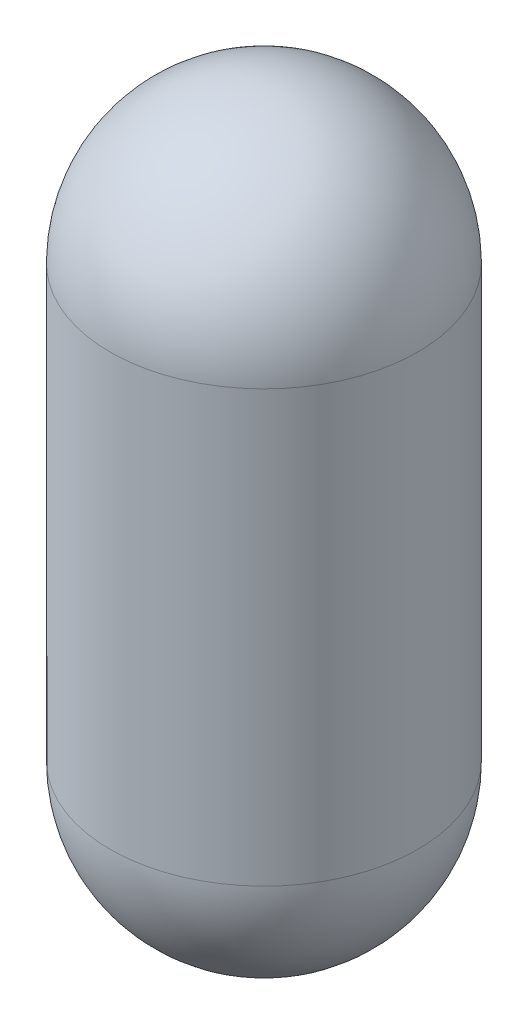
SolidWorks part; units mm, degrees
ref_plane "Front Plane" through (0, 0, 0) normal (0, 0, 1) x (1, 0, 0)
ref_plane "Top Plane" through (0, 0, 0) normal (0, 1, 0) x (1, 0, 0)
ref_plane "Right Plane" through (0, 0, 0) normal (1, 0, 0) x (0, 0, -1)
sketch "Sketch1" plane through (0, 0, 0) normal (0, 0, 1) x (1, 0, 0)
  line L0 (125, 475) -> (125, -125) construction
  line L2 (0, 0) -> (0, 350)
  line L5 (10, 0) -> (10, 350)
  line L6 (125, 465) -> (125, 475)
  line L7 (125, -115) -> (125, -125)
  arc A0 (125, 475) -> (0, 350) centre (125, 350) ccw
  arc A1 (0, 0) -> (125, -125) centre (125, 0) ccw
  arc A2 (10, 0) -> (125, -115) centre (125, 0) ccw
  arc A3 (125, 465) -> (10, 350) centre (125, 350) ccw
  dimension "D1" = 600
  dimension "D2" = 125
  dimension "D3" = 10
revolve "Revolve1" add sketch "Sketch1" angle 360 about L0
